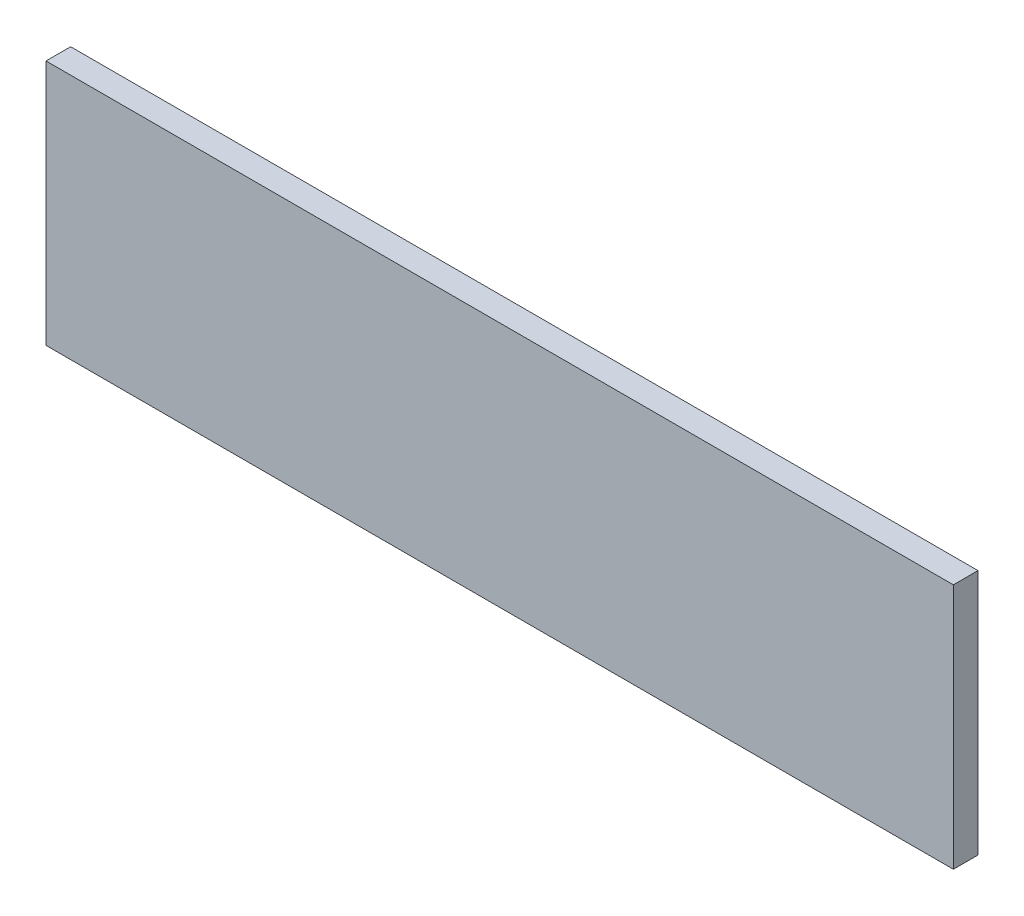
SolidWorks part; units mm, degrees
ref_plane "Alzado" through (0, 0, 0) normal (0, 0, 1) x (1, 0, 0)
ref_plane "Planta" through (0, 0, 0) normal (0, 1, 0) x (1, 0, 0)
ref_plane "Vista lateral" through (0, 0, 0) normal (1, 0, 0) x (0, 0, -1)
sketch "Croquis1" plane through (0, 0, 0) normal (1, 0, 0) x (0, 0, -1)
  line L1 (1.5, -15) -> (-1.5, -15)
  line L2 (1.5, -15) -> (1.5, 15)
  line L3 (1.5, 15) -> (-1.5, 15)
  line L4 (-1.5, -15) -> (-1.5, 15)
  line L5 (1.5, -15) -> (-1.5, 15) construction
  line L6 (1.5, 15) -> (-1.5, -15) construction
  point P0 (0, 0)
  dimension "D1" = 3
extrude "Saliente-Extruir1" add sketch "Croquis1" along normal blind 110.49
